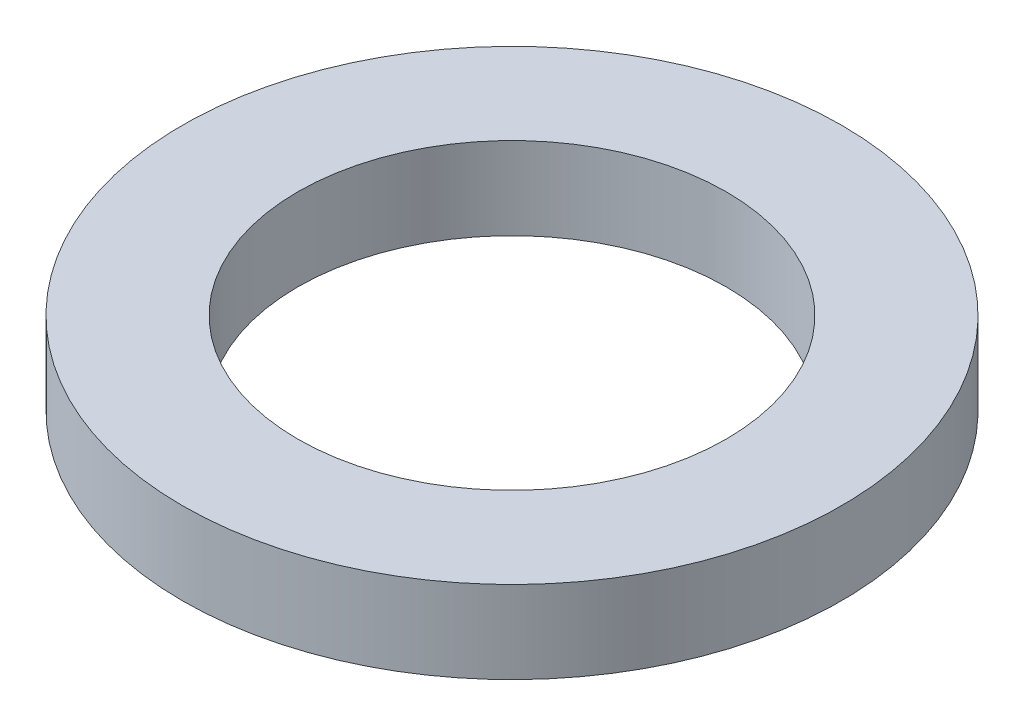
SolidWorks part; units mm, degrees
ref_plane "Front Plane" through (0, 0, 0) normal (0, 0, 1) x (1, 0, 0)
ref_plane "Top Plane" through (0, 0, 0) normal (0, 1, 0) x (1, 0, 0)
ref_plane "Right Plane" through (0, 0, 0) normal (1, 0, 0) x (0, 0, -1)
sketch "Sketch1" plane through (0, 0, 0) normal (0, 1, 0) x (1, 0, 0)
  circle A0 centre (0, 0) radius 4
  circle A1 centre (0, 0) radius 2.6
  dimension "D1" = 5.2
  dimension "D2" = 8
extrude "Boss-Extrude1" add sketch "Sketch1" along normal blind 1
